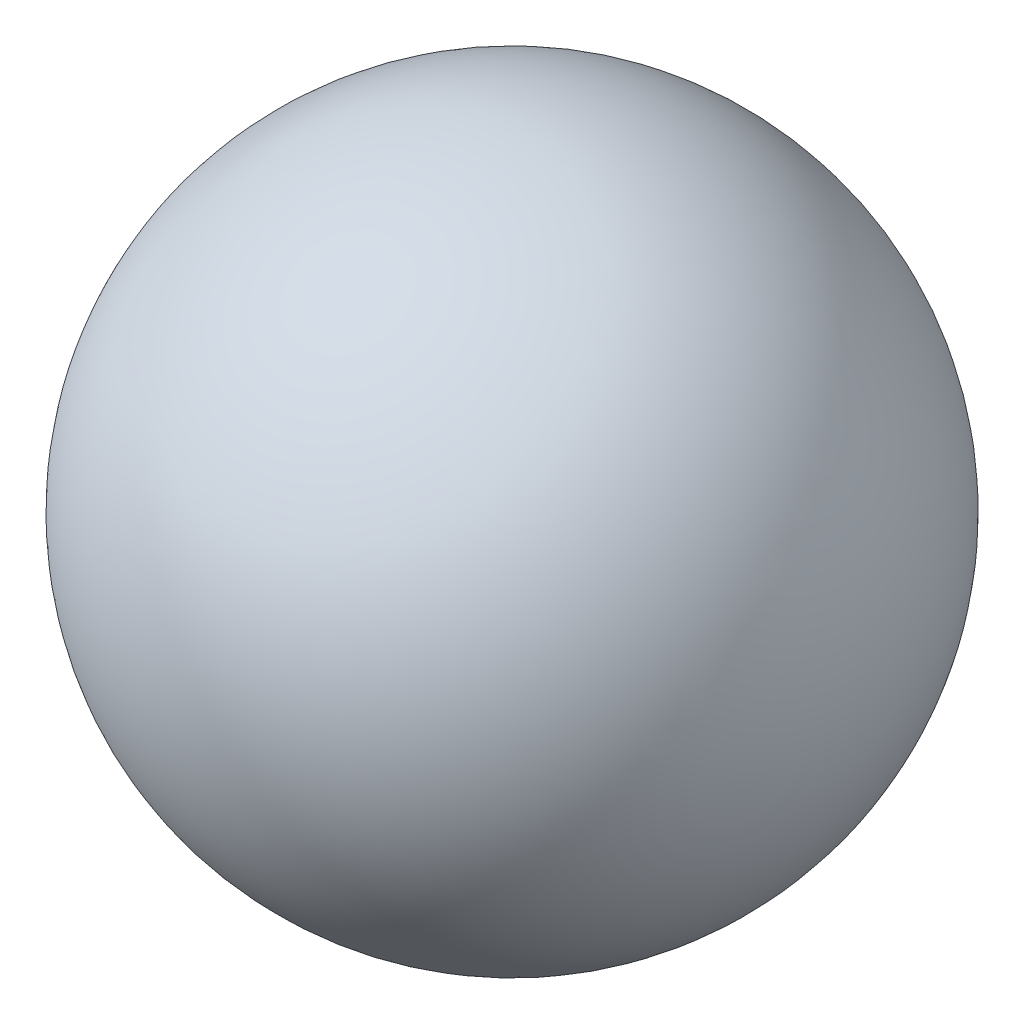
SolidWorks part; units mm, degrees
ref_plane "Front Plane" through (0, 0, 0) normal (0, 0, 1) x (1, 0, 0)
ref_plane "Top Plane" through (0, 0, 0) normal (0, 1, 0) x (1, 0, 0)
ref_plane "Right Plane" through (0, 0, 0) normal (1, 0, 0) x (0, 0, -1)
sketch "Sketch2" plane through (0, 0, 0) normal (0, 0, 1) x (1, 0, 0)
  line L0 (1809.0658, 0) -> (-1809.0658, 0)
  arc A0 (1809.0658, 0) -> (-1809.0658, 0) centre (0, 0) ccw
  dimension "D1" = 3618.1316
revolve "Revolve1" add sketch "Sketch2" angle 360 about L0
